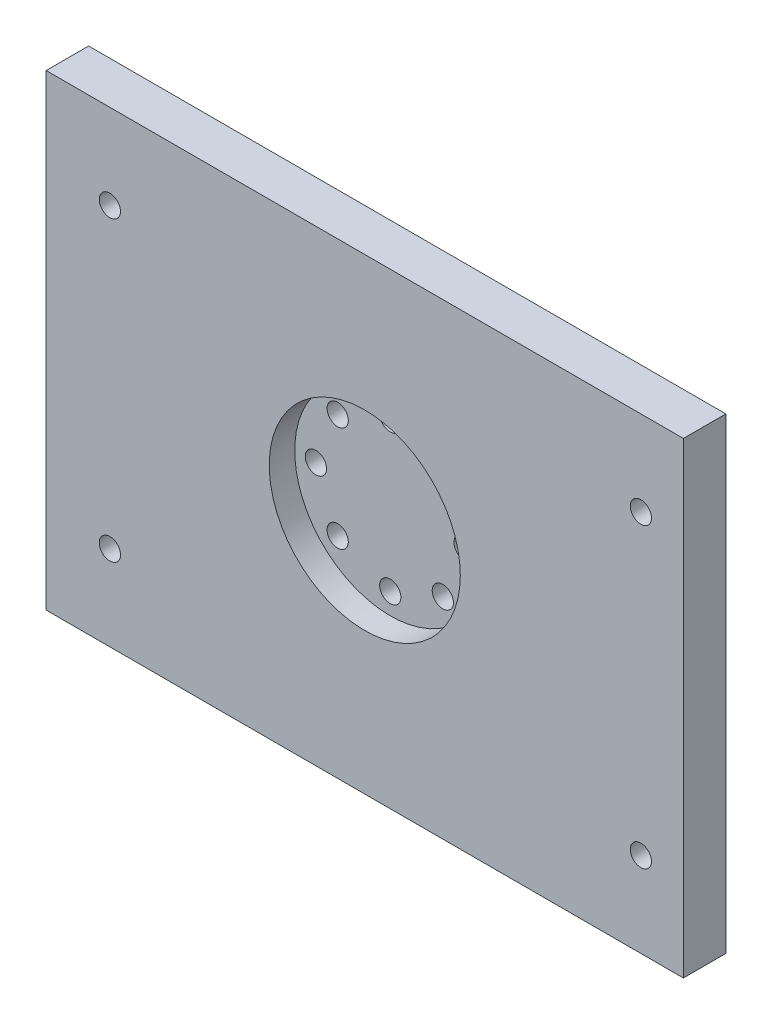
SolidWorks part; units mm, degrees
ref_plane "Front Plane" through (0, 0, 0) normal (0, 0, 1) x (1, 0, 0)
ref_plane "Top Plane" through (0, 0, 0) normal (0, 1, 0) x (1, 0, 0)
ref_plane "Right Plane" through (0, 0, 0) normal (1, 0, 0) x (0, 0, -1)
sketch "Sketch1" plane through (0, 0, 0) normal (0, 0, 1) x (1, 0, 0)
  line L1 (-125.3234, 54.1791) -> (24.6766, 54.1791)
  line L2 (-125.3234, 54.1791) -> (-125.3234, -55.8209)
  line L3 (-125.3234, -55.8209) -> (24.6766, -55.8209)
  line L4 (24.6766, 54.1791) -> (24.6766, -55.8209)
  dimension "D1" = 110
  dimension "D2" = 150
extrude "Boss-Extrude2" add sketch "Sketch1" along normal blind 10
sketch "Sketch2" plane through (0, 0, 10) normal (0, 0, 1) x (1, 0, 0)
  circle A0 centre (-50.3234, 0) radius 22.49
extrude "Cut-Extrude1" cut sketch "Sketch2" against normal blind 6
sketch "Sketch3" plane through (0, 0, 4) normal (0, 0, 1) x (1, 0, 0)
  circle A0 centre (-50.3234, 0) radius 17.5 construction
  point P3 (-50.3234, 17.5)
  point P4 (-50.3234, -17.5)
  point P5 (-32.8234, 0)
  point P6 (-67.8234, 0)
  point P11 (-62.6978, 12.3744)
  point P12 (-37.949, 12.3744)
  point P13 (-37.949, -12.3744)
  point P14 (-62.6978, -12.3744)
  dimension "D2" = 17.5
hole_wizard "Ø5.0mm Dowel Hole1" positions "3DSketch1" profile "Sketch4" hole size "Ø5.0" standard "ANSI Metric" end condition through all
sketch3d "3DSketch1"
  point P0 (-50.3234, 17.5, 4)
  point P3 (-62.6978, 12.3744, 4)
  point P6 (-67.8234, 0, 4)
  point P9 (-62.6978, -12.3744, 4)
  point P12 (-50.3234, -17.5, 4)
  point P15 (-37.949, -12.3744, 4)
  point P18 (-32.8234, 0, 4)
  point P21 (-37.949, 12.3744, 4)
sketch "Sketch4" plane through (-50.3234, 17.5, 4) normal (1, 0, 0) x (0, -1, 0)
  line L0 (0, 0) -> (0, 4)
  line L1 (0, 4) -> (2.5, 4)
  line L2 (2.5, 4) -> (2.5, 0)
  line L5 (2.5, 0) -> (0, 0)
  line L11 (0, -6.35) -> (0, 107.95) construction
  dimension "Thru Hole Dia." = 5
  dimension "Thru Hole Depth" = 4
sketch "Sketch5" plane through (0, 0, 10) normal (0, 0, 1) x (1, 0, 0)
  line L0 (24.6766, 54.1791) -> (-125.3234, 54.1791) construction
  line L1 (-125.3234, -55.8209) -> (24.6766, -55.8209) construction
  line L2 (-125.3234, 54.1791) -> (-125.3234, -55.8209) construction
  line L3 (24.6766, -55.8209) -> (24.6766, 54.1791) construction
  point P0 (-110.3234, 34.1791)
  point P1 (14.6766, 34.1791)
  point P2 (14.6766, -35.8209)
  point P3 (-110.3234, -35.8209)
  dimension "D1" = 20
  dimension "D2" = 20
  dimension "D3" = 15
  dimension "D4" = 15
  dimension "D5" = 20
  dimension "D6" = 20
  dimension "D7" = 10
  dimension "D8" = 10
hole_wizard "Ø5.0mm Dowel Hole2" positions "3DSketch2" profile "Sketch6" hole size "Ø5.0" standard "ANSI Metric" end condition through all
sketch3d "3DSketch2"
  point P0 (-110.3234, 34.1791, 10)
  point P3 (14.6766, 34.1791, 10)
  point P6 (14.6766, -35.8209, 10)
  point P9 (-110.3234, -35.8209, 10)
sketch "Sketch6" plane through (-110.3234, 34.1791, 10) normal (1, 0, 0) x (0, -1, 0)
  line L0 (0, 0) -> (0, 10)
  line L1 (0, 10) -> (2.5, 10)
  line L2 (2.5, 10) -> (2.5, 0)
  line L5 (2.5, 0) -> (0, 0)
  line L11 (0, -6.35) -> (0, 107.95) construction
  dimension "Thru Hole Dia." = 5
  dimension "Thru Hole Depth" = 10
